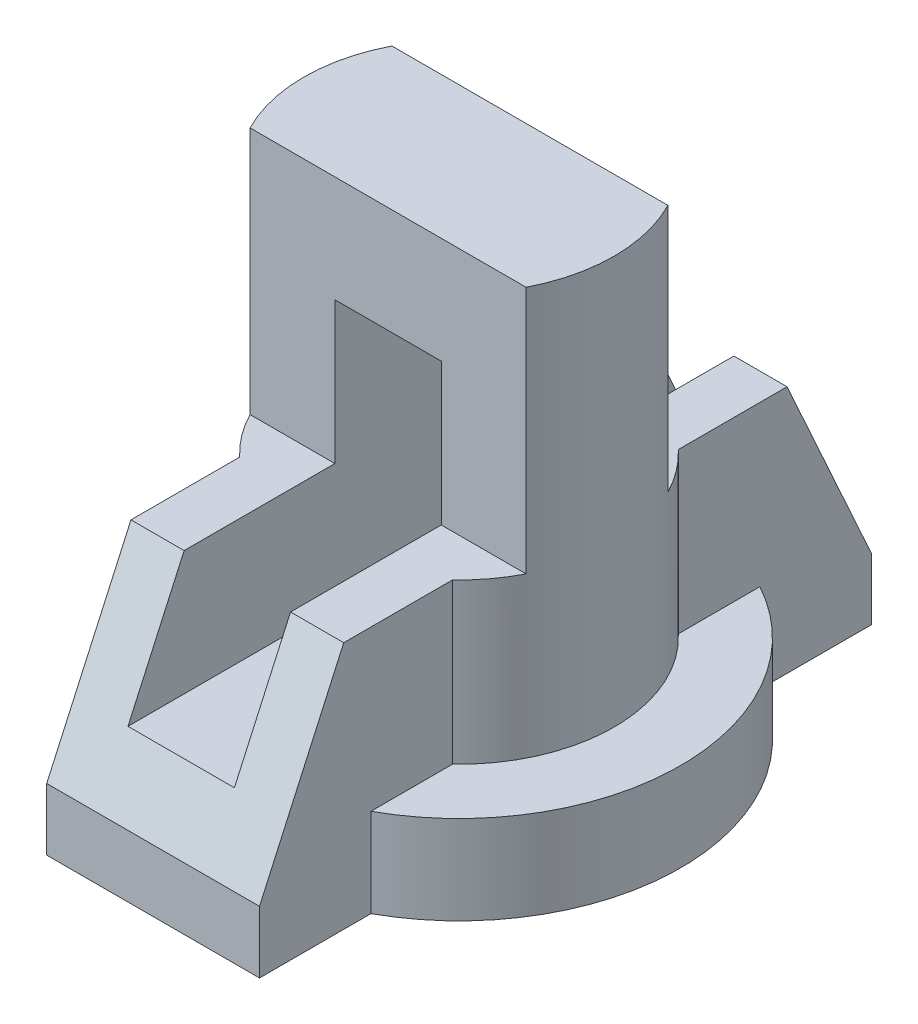
SolidWorks part; units mm, degrees
ref_plane "Front Plane" through (0, 0, 0) normal (0, 0, 1) x (1, 0, 0)
ref_plane "Top Plane" through (0, 0, 0) normal (0, 1, 0) x (1, 0, 0)
ref_plane "Right Plane" through (0, 0, 0) normal (1, 0, 0) x (0, 0, -1)
sketch "Sketch1" plane through (0, 0, 0) normal (0, 1, 0) x (1, 0, 0)
  line L0 (-49.8297, 0) -> (51.5781, 0) construction
  line L1 (0, 37.0808) -> (0, -40.7234) construction
  circle A0 centre (0, 0) radius 25
  dimension "D1" = 50
extrude "Boss-Extrude1" add sketch "Sketch1" along normal blind 10
sketch "Sketch2" plane through (0, 10, 0) normal (0, 1, 0) x (1, 0, 0)
  circle A0 centre (0, 0) radius 17.5
  dimension "D1" = 35
extrude "Boss-Extrude2" add sketch "Sketch2" along normal blind 18
sketch "Sketch3" plane through (0, 28, 0) normal (0, 1, 0) x (1, 0, 0)
  line L0 (-15.5644, -8) -> (15.5644, -8)
  line L1 (-51.7718, 0) -> (45.1992, 0) construction
  line L2 (15.5644, 8) -> (-15.5644, 8)
  circle A0 centre (0, 0) radius 17.5 construction
  circle A1 centre (0, 0) radius 17.5 construction
  arc A2 (-15.5644, 8) -> (-15.5644, -8) centre (0, 0) ccw
  arc A3 (15.5644, -8) -> (15.5644, 8) centre (0, 0) ccw
  dimension "D1" = 16
extrude "Boss-Extrude3" add sketch "Sketch3" along normal blind 28
sketch "Sketch4" plane through (0, 0, 0) normal (1, 0, 0) x (0, 0, -1)
  line L0 (-45.5268, 0) -> (50.2834, 0) construction
  line L1 (0, 64.6366) -> (0, -19.5087) construction
  line L9 (34.5, 0) -> (34.5, 7)
  line L13 (34.5, 7) -> (25, 28)
  line L17 (-34.5, 0) -> (-34.5, 7)
  line L18 (-34.5, 7) -> (-25, 28)
  line L19 (-8, 28) -> (-17.5, 28) construction
  line L25 (-25, 28) -> (25, 28)
  line L26 (-34.5, 0) -> (34.5, 0)
  dimension "D1" = 7
  dimension "D2" = 50
  dimension "D3" = 69
extrude "Boss-Extrude6" add sketch "Sketch4" along normal mid plane 24
sketch "Sketch5" plane through (0, 0, 0) normal (0, 0, 1) x (1, 0, 0)
  line L0 (0, 63.1644) -> (0, -18.0365) construction
  line L1 (-37.3728, 0) -> (50.8496, 0) construction
  line L2 (-15.5644, 56) -> (15.5644, 56) construction
  line L3 (-6, 14) -> (6, 14)
  line L4 (-6, 14) -> (-6, 44)
  line L5 (-6, 44) -> (6, 44)
  line L6 (6, 14) -> (6, 44)
  line L7 (-6, 14) -> (6, 44) construction
  line L8 (-6, 44) -> (6, 14) construction
  point P5 (0, 29)
  dimension "D1" = 12
  dimension "D2" = 30
  dimension "D3" = 12
extrude "Cut-Extrude3" cut sketch "Sketch5" against normal through all both and the other way through all
